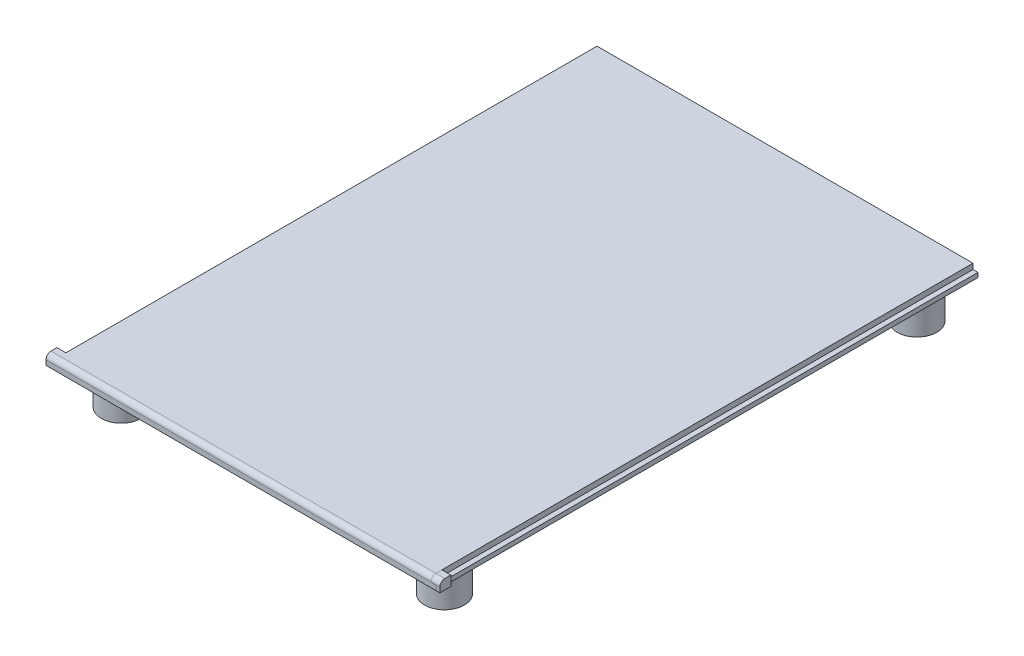
SolidWorks part; units mm, degrees
ref_plane "Front Plane" through (0, 0, 0) normal (0, 0, 1) x (1, 0, 0)
ref_plane "Top Plane" through (0, 0, 0) normal (0, 1, 0) x (1, 0, 0)
ref_plane "Right Plane" through (0, 0, 0) normal (1, 0, 0) x (0, 0, -1)
sketch "Sketch1" plane through (0, 0, 0) normal (0, 1, 0) x (1, 0, 0)
  line L1 (0, 0) -> (77.6, 0)
  line L2 (0, 0) -> (0, 109)
  line L3 (0, 109) -> (77.6, 109)
  line L4 (77.6, 0) -> (77.6, 109)
  dimension "D1" = 77.6
  dimension "D2" = 109
extrude "Boss-Extrude1" add sketch "Sketch1" along normal blind 2
sketch "Sketch2" plane through (0, 2, 0) normal (0, 1, 0) x (1, 0, 0)
  line L0 (0, 0) -> (77.6, 0) construction
  line L1 (77.6, 109) -> (76.6, 109)
  line L2 (77.6, 109) -> (77.6, 0)
  line L3 (77.6, 0) -> (76.6, 0)
  line L4 (76.6, 109) -> (76.6, 0)
  line L5 (77.6, 109) -> (0, 109) construction
  line L6 (0, 0) -> (1, 0)
  line L7 (0, 0) -> (0, 109)
  line L8 (0, 109) -> (1, 109)
  line L9 (1, 0) -> (1, 109)
  dimension "D1" = 1
  dimension "D2" = 1
extrude "Cut-Extrude1" cut sketch "Sketch2" against normal blind 1.1
sketch "Sketch3" plane through (0, 2, 0) normal (0, 1, 0) x (1, 0, 0)
  circle A0 centre (6, 103.3195) radius 4
  circle A1 centre (6, 8.3195) radius 4
  circle A2 centre (71, 8.3195) radius 4
  circle A3 centre (71, 103.3195) radius 4
  circle A4 centre (6, 103.3195) radius 1.5
  circle A5 centre (71, 103.3195) radius 1.5
  circle A6 centre (71, 8.3195) radius 1.5
  circle A7 centre (6, 8.3195) radius 1.5
  dimension "D1" = 3
  dimension "D2" = 3
  dimension "3" = 3
  dimension "D3" = 3
  dimension "D4" = 8
  dimension "D5" = 8
  dimension "D6" = 8
  dimension "D7" = 8
  dimension "D8" = 65
  dimension "D9" = 95
extrude "Boss-Extrude2" add sketch "Sketch3" against normal blind 10
sketch "Sketch4" plane through (0, 2, 0) normal (0, 1, 0) x (1, 0, 0)
  line L0 (1, 0) -> (1, 109) construction
  line L1 (1, 2.2) -> (-0.8, 2.2)
  line L2 (1, 2.2) -> (1, 0)
  line L3 (1, 0) -> (-0.8, 0)
  line L4 (-0.8, 2.2) -> (-0.8, 0)
  dimension "D1" = 1.8
  dimension "D2" = 2.2
extrude "Boss-Extrude3" add sketch "Sketch4" against normal blind 2
sketch "Sketch5" plane through (0, 2, 0) normal (0, 1, 0) x (1, 0, 0)
  line L0 (76.6, 109) -> (76.6, 0) construction
  line L1 (76.6, 2.2) -> (78.4, 2.2)
  line L2 (76.6, 2.2) -> (76.6, 0)
  line L3 (76.6, 0) -> (78.4, 0)
  line L4 (78.4, 2.2) -> (78.4, 0)
  line L5 (-0.8, 0) -> (76.6, 0) construction
  dimension "D1" = 1.8
  dimension "D2" = 2.2
  dimension "D3" = 0
extrude "Boss-Extrude4" add sketch "Sketch5" against normal blind 2 separate body
fillet "Fillet1" radius 1 1 edges at (37.9, 2, 0)
fillet "Fillet2" radius 1 1 edges at (77.5, 2, 0)
